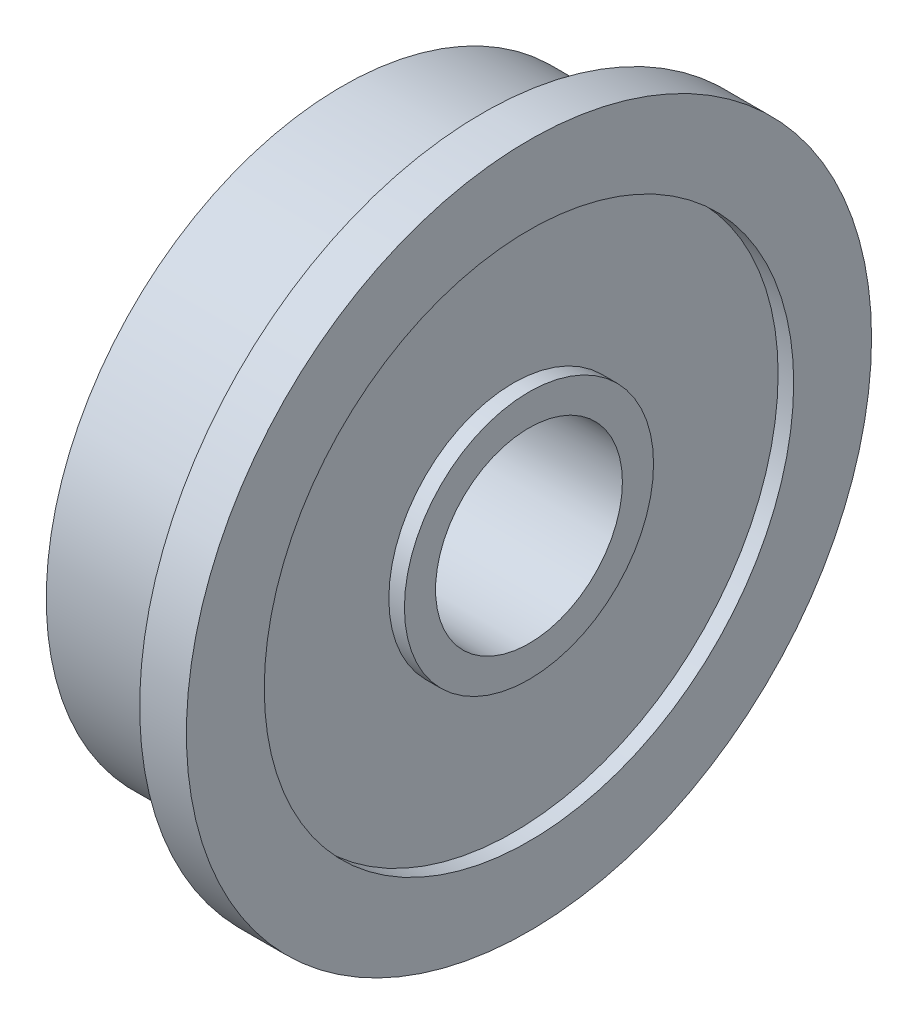
SolidWorks part; units mm, degrees
material "AISI 304"
ref_plane "Front Plane" through (0, 0, 0) normal (0, 0, 1) x (1, 0, 0)
ref_plane "Top Plane" through (0, 0, 0) normal (0, 1, 0) x (1, 0, 0)
ref_plane "Right Plane" through (0, 0, 0) normal (1, 0, 0) x (0, 0, -1)
sketch "Sketch1" plane through (0, 0, 0) normal (0, 0, 1) x (1, 0, 0)
  line L0 (-4.5, 3) -> (1.5, 3)
  line L1 (1.5, 3) -> (1.5, 4)
  line L2 (1.5, 11) -> (0, 11)
  line L3 (0, 11) -> (0, 9.5)
  line L4 (0, 9.5) -> (-4.5, 9.5)
  line L5 (-4.5, 9.5) -> (-4.5, 8.5)
  line L6 (-4.5, 4) -> (-4.5, 3)
  line L7 (-4.5, 8.5) -> (-4, 8.5)
  line L8 (1.5, 8.5) -> (1.5, 11)
  line L9 (-4.5, 4) -> (-4, 4)
  line L10 (-4, 8.5) -> (-4, 4)
  line L11 (1.5, 8.5) -> (1, 8.5)
  line L12 (0, 0) -> (0, 9.5) construction
  line L13 (1.5, 4) -> (1, 4)
  line L14 (1, 8.5) -> (1, 4)
  line L15 (0, 0) -> (-10.1414, 0) construction
  dimension "D1" = 1.5
  dimension "D2" = 8
  dimension "D3" = 6
  dimension "D4" = 19
  dimension "D5" = 22
  dimension "D6" = 0.5
  dimension "D7" = 6
revolve "Revolve1" add sketch "Sketch1" angle 360 about L15
